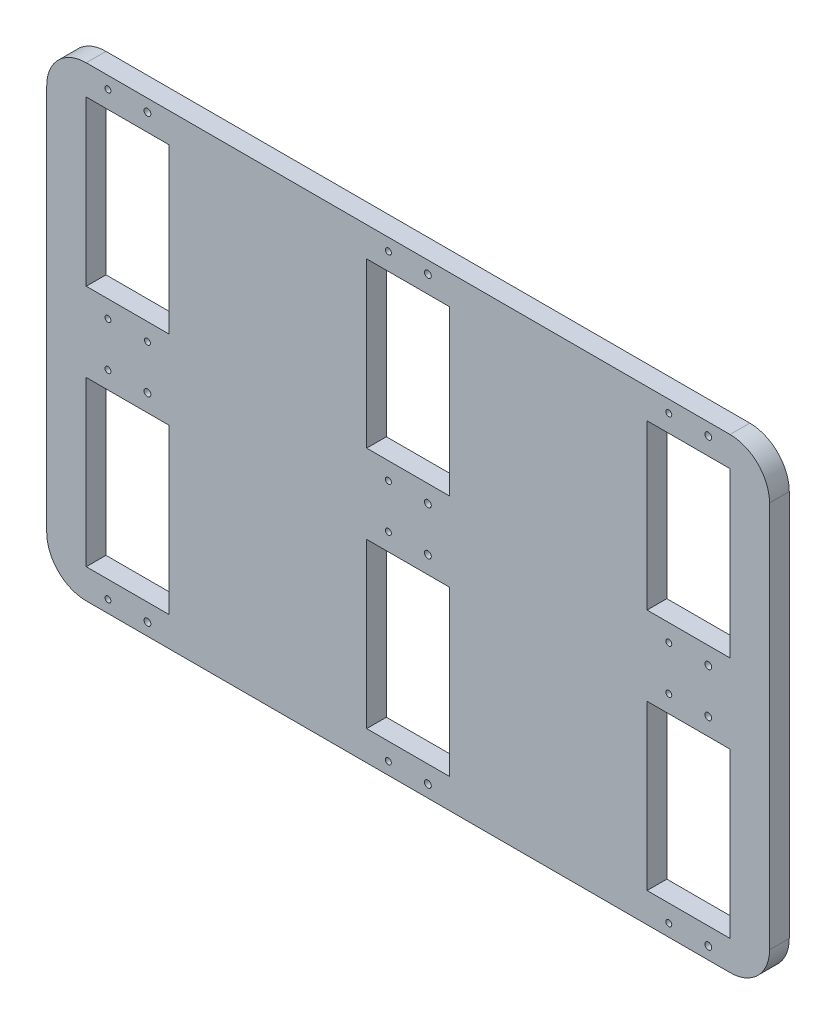
SolidWorks part; units mm, degrees
ref_plane "Front Plane" through (0, 0, 0) normal (0, 0, 1) x (1, 0, 0)
ref_plane "Top Plane" through (0, 0, 0) normal (0, 1, 0) x (1, 0, 0)
ref_plane "Right Plane" through (0, 0, 0) normal (1, 0, 0) x (0, 0, -1)
sketch "Sketch1" plane through (0, 0, 0) normal (0, 0, 1) x (1, 0, 0)
  line L1 (0, 0) -> (-183, 0)
  line L2 (0, 0) -> (0, 118)
  line L3 (0, 118) -> (-183, 118)
  line L4 (-183, 0) -> (-183, 118)
  line L5 (-173, 49) -> (-152, 49)
  line L6 (-173, 49) -> (-173, 7.5)
  line L7 (-173, 7.5) -> (-152, 7.5)
  line L8 (-152, 49) -> (-152, 7.5)
  line L9 (-102, 49) -> (-81, 49)
  line L10 (-102, 49) -> (-102, 7.5)
  line L11 (-102, 7.5) -> (-81, 7.5)
  line L12 (-81, 49) -> (-81, 7.5)
  line L13 (-31, 49) -> (-10, 49)
  line L14 (-31, 49) -> (-31, 7.5)
  line L15 (-31, 7.5) -> (-10, 7.5)
  line L16 (-10, 49) -> (-10, 7.5)
  line L17 (-173, 110.5) -> (-152, 110.5)
  line L18 (-173, 110.5) -> (-173, 69)
  line L19 (-173, 69) -> (-152, 69)
  line L20 (-152, 110.5) -> (-152, 69)
  line L21 (-102, 110.5) -> (-81, 110.5)
  line L22 (-102, 110.5) -> (-102, 69)
  line L23 (-102, 69) -> (-81, 69)
  line L24 (-81, 110.5) -> (-81, 69)
  line L25 (-31, 110.5) -> (-10, 110.5)
  line L26 (-31, 110.5) -> (-31, 69)
  line L27 (-31, 69) -> (-10, 69)
  line L28 (-10, 110.5) -> (-10, 69)
  point P32 (-173, 89.75)
  dimension "D1" = 41.5
  dimension "D2" = 41.5
  dimension "D3" = 41.5
  dimension "D4" = 41.5
  dimension "D5" = 41.5
  dimension "D6" = 41.5
  dimension "D7" = 10
  dimension "D8" = 50
  dimension "D9" = 21
  dimension "D10" = 21
  dimension "D11" = 21
  dimension "D12" = 21
  dimension "D13" = 21
  dimension "D14" = 21
  dimension "D15" = 50
  dimension "D16" = 10
  dimension "D17" = 7.5
  dimension "D18" = 10
  dimension "D19" = 50
  dimension "D20" = 50
  dimension "D21" = 7.5
  dimension "D22" = 20
  dimension "D23" = 7.5
  dimension "D24" = 7.5
extrude "Boss-Extrude1" add sketch "Sketch1" along normal blind 5
sketch "Sketch2" plane through (0, 0, 5) normal (0, 0, 1) x (1, 0, 0)
  circle A0 centre (-167.5, 114.9) radius 0.75
  circle A1 centre (-157.5, 114.9) radius 0.8653
  circle A2 centre (-167.5, 64.6) radius 0.75
  circle A3 centre (-157.5, 64.6) radius 0.75
  circle A4 centre (-96.5, 114.9) radius 0.75
  circle A5 centre (-86.5, 114.9) radius 0.8653
  circle A6 centre (-96.5, 64.6) radius 0.75
  circle A7 centre (-86.5, 64.6) radius 0.8653
  circle A8 centre (-96.5, 53.4) radius 0.75
  circle A9 centre (-86.5, 53.4) radius 0.8653
  circle A10 centre (-25.5, 114.9) radius 0.75
  circle A11 centre (-15.5, 114.9) radius 0.8653
  circle A12 centre (-25.5, 64.6) radius 0.75
  circle A13 centre (-15.5, 64.6) radius 0.8653
  circle A14 centre (-25.5, 53.4) radius 0.75
  circle A15 centre (-15.5, 53.4) radius 0.8653
  circle A16 centre (-25.5, 3.1) radius 0.75
  circle A17 centre (-15.5, 3.1) radius 0.8653
  circle A18 centre (-96.5, 3.1) radius 0.75
  circle A19 centre (-86.5, 3.1) radius 0.8653
  circle A20 centre (-167.5, 3.1) radius 0.75
  circle A21 centre (-157.5, 3.1) radius 0.8653
  circle A22 centre (-167.5, 53.4) radius 0.75
  circle A23 centre (-157.5, 53.4) radius 0.8653
  point P34 (-158.1408, 114.3739)
  point P37 (-167.513, 66.4764)
  point P40 (-158.1408, 66.4764)
  point P45 (-96.5932, 114.3739)
  point P46 (-86.0767, 114.3739)
  point P51 (-96.5932, 66.4764)
  point P52 (-86.0767, 66.4764)
  point P57 (-96.5932, 51.5883)
  point P58 (-86.0767, 51.5883)
  point P63 (-26.1424, 114.3739)
  point P64 (-15.6275, 114.3739)
  point P69 (-26.1424, 66.4764)
  point P70 (-15.6275, 66.4764)
  point P75 (-26.1424, 51.5883)
  point P76 (-15.6275, 51.5883)
  point P81 (-26.1424, 4.6154)
  point P82 (-15.6275, 4.6154)
  point P87 (-96.5932, 4.6154)
  point P88 (-86.0767, 4.6154)
  point P93 (-167.513, 4.6154)
  point P94 (-158.1408, 4.6154)
  point P99 (-169.6256, 53.4281)
  point P100 (-158.1408, 53.4281)
  point P101 (0, 0)
  point P102 (0, 0)
  dimension "D1" = 1.5
  dimension "D2" = 10
  dimension "D3" = 10
  dimension "D4" = 10
  dimension "D8" = 10
  dimension "D11" = 10
  dimension "D13" = 10
  dimension "D15" = 10
  dimension "D17" = 10
  dimension "D19" = 10
  dimension "D21" = 10
  dimension "D23" = 10
  dimension "D25" = 10
  dimension "D26" = 50.3
  dimension "D27" = 50.3
  dimension "D29" = 50.3
  dimension "D31" = 50.3
  dimension "D33" = 50.3
  dimension "D35" = 50.3
  dimension "D37" = 50.3
extrude "Cut-Extrude1" cut sketch "Sketch2" against normal blind 5
fillet "Fillet5" radius 10 1 edges at (-183, 118, 2.5)
fillet "Fillet6" radius 10 1 edges at (-183, 0, 2.5)
fillet "Fillet7" radius 10 1 edges at (0, 118, 2.5)
fillet "Fillet8" radius 10 1 edges at (0, 0, 2.5)
